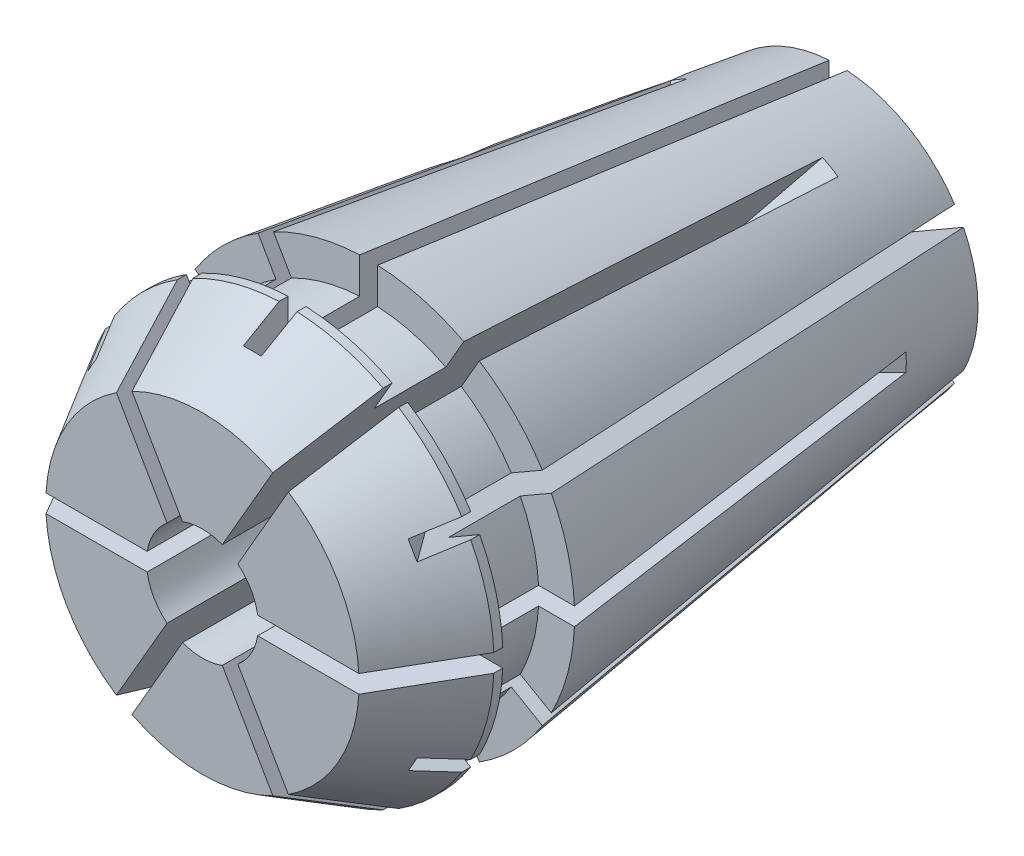
SolidWorks part; units mm, degrees
material "Plain Carbon Steel"
ref_plane "Front Plane" through (0, 0, 0) normal (0, 0, 1) x (1, 0, 0)
ref_plane "Top Plane" through (0, 0, 0) normal (0, 1, 0) x (1, 0, 0)
ref_plane "Right Plane" through (0, 0, 0) normal (1, 0, 0) x (0, 0, -1)
sketch "Sketch1" plane through (0, 0, 0) normal (0, 1, 0) x (1, 0, 0)
  line L0 (0, -9.017) -> (0, 9.017) construction
  line L1 (-5.842, 0) -> (5.842, 0) construction
  line L2 (-1.5875, -9.017) -> (1.5875, -9.017) construction
  point P4 (0, 0)
  point P8 (0, 0)
  point P10 (0, 0)
  point P11 (0, -9.017)
sketch "Sketch2" plane through (0, 0, 0) normal (0, 1, 0) x (1, 0, 0)
  line L0 (0, 9.017) -> (0, -9.017) construction
  line L1 (0, -9.017) -> (4.445, -9.017) construction
  line L2 (4.445, -9.017) -> (5.842, -6.5875)
  line L4 (4.826, -6.3335) -> (4.826, -4.3015)
  line L5 (4.826, -4.3015) -> (5.842, -4.3015)
  line L6 (5.842, -4.3015) -> (3.9678, 9.017)
  line L7 (3.9678, 9.017) -> (0, 9.017) construction
  line L8 (5.842, -6.5875) -> (5.842, -9.6909) construction
  line L9 (-5.842, -4.3015) -> (5.842, -4.3015) construction
  line L10 (1.5875, 9.017) -> (1.5875, -9.017)
  line L11 (3.9678, 9.017) -> (1.5875, 9.017)
  line L12 (4.445, -9.017) -> (1.5875, -9.017)
  line L13 (-1.5875, 0) -> (1.5875, 0) construction
  line L14 (5.842, -4.3015) -> (5.842, 9.017) construction
  line L15 (-4.445, -9.017) -> (4.445, -9.017) construction
  line L16 (-4.826, -5.3175) -> (4.826, -5.3175) construction
  line L17 (4.826, -6.3335) -> (5.842, -6.3335)
  line L18 (5.842, -6.3335) -> (5.842, -6.5875)
  point P4 (0, 0)
  point P14 (0, -4.3015)
  point P17 (0, 0)
  point P25 (0, -9.017)
  point P26 (0, -5.3175)
  dimension "Max Grip Range" = 3.175
  dimension "D1" = 8.01
  dimension "D2" = 29.9
  dimension "D3" = 8.89
  dimension "D4" = 9.652
  dimension "D5" = 2.032
  dimension "D6" = 0.254
revolve "Revolve1" add sketch "Sketch2" angle 360 about L0
sketch "Sketch3" plane through (0, 0, 0) normal (1, 0, 0) x (0, 0, -1)
  line L0 (9.017, 1.5875) -> (-3.937, 1.5875) construction
  line L1 (-3.937, 1.5875) -> (-7.6059, 5.2564) construction
  line L2 (-6.5875, 5.842) -> (-9.017, 4.445) construction
  line L3 (-7.6059, 5.2564) -> (-7.6059, 26.9875)
  line L4 (-7.6059, 26.9875) -> (9.017, 26.9875)
  line L5 (9.017, 26.9875) -> (9.017, 1.5875) construction
  line L7 (9.017, 26.9875) -> (9.017, 0.3175)
  line L8 (9.017, 0.3175) -> (-2.667, 0.3175)
  line L9 (-2.667, 0.3175) -> (-7.6059, 5.2564)
  dimension "D1" = 135
  dimension "D2" = 12.954
  dimension "D3" = 25.4
  dimension "D4" = 1.27
extrude "Cut-Extrude3" cut sketch "Sketch3" against normal mid plane 0.508
pattern_circular "CirPattern1" count 6 over 360 about axis through (0, 0, 0) along (0, 0, 1) of "Cut-Extrude3"
sketch "Sketch4" plane through (0, 0, 0) normal (0, 1, 0) x (1, 0, 0)
  line L0 (1.5875, -9.017) -> (1.5875, 3.937) construction
  line L1 (1.5875, 3.937) -> (4.3009, 6.6504) construction
  line L2 (5.842, -4.3015) -> (3.9678, 9.017) construction
  line L3 (4.3009, 6.6504) -> (26.9875, 6.6504)
  line L4 (26.9875, 6.6504) -> (26.9875, -9.017)
  line L5 (26.9875, -9.017) -> (1.5875, -9.017)
  line L6 (4.3009, 6.6504) -> (0.3175, 2.667)
  line L7 (0.3175, 2.667) -> (0.3175, -9.017)
  line L8 (0.3175, -9.017) -> (1.5875, -9.017)
  dimension "D1" = 12.954
  dimension "D2" = 135
  dimension "D3" = 25.4
  dimension "D4" = 1.27
extrude "Cut-Extrude4" cut sketch "Sketch4" against normal mid plane 0.508
pattern_circular "CirPattern2" count 6 over 360 about axis through (0, 0, 0) along (0, 0, 1) of "Cut-Extrude4"
sketch "Sketch5" plane through (0, 0, 0) normal (0, 0, 1) x (1, 0, 0)
  line L1 (0, 0) -> (1.5875, 0) construction
  circle A0 centre (0, 0) radius 1.5875 construction
  point P4 (0, -1.5875)
  dimension "D1" = 3.175
equation "\"Max Grip Range@Sketch2\"=\"Max Grip Range@Sketch1\""
equation "\"D1@Sketch5\"=\"Max Grip Range@Sketch1\""
